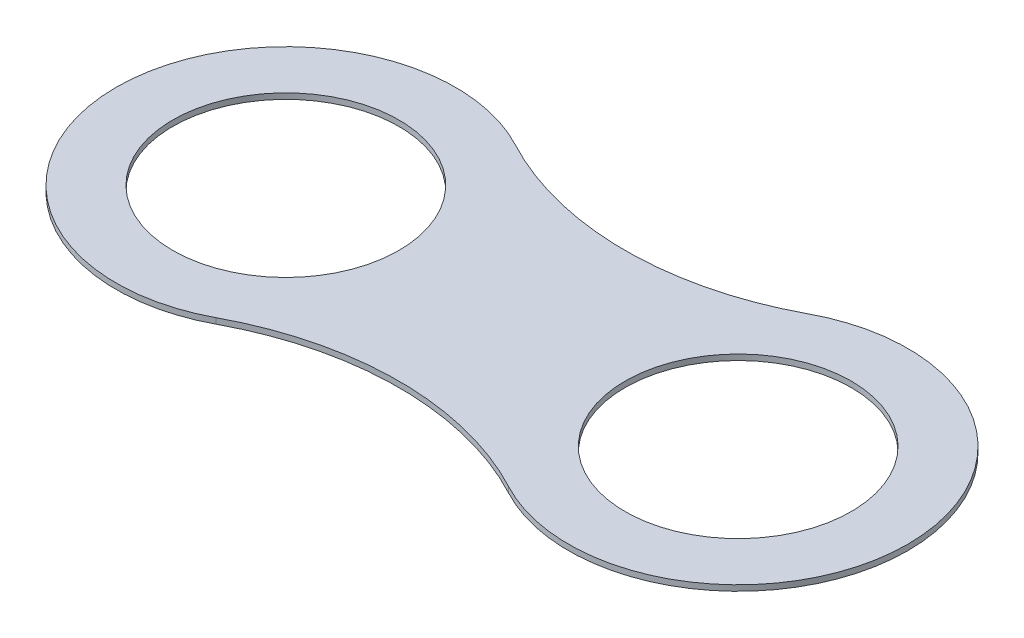
SolidWorks part; units mm, degrees
ref_plane "Face" through (0, 0, 0) normal (0, 0, 1) x (1, 0, 0)
ref_plane "Dessus" through (0, 0, 0) normal (0, 1, 0) x (1, 0, 0)
ref_plane "Droite" through (0, 0, 0) normal (1, 0, 0) x (0, 0, -1)
sketch "Esquisse1" plane through (0, 0, 0) normal (0, 1, 0) x (1, 0, 0)
  line L0 (0, 0) -> (800, 0) construction
  line L1 (400, 200) -> (400, 0) construction
  line L2 (0, 0) -> (-300, 0) construction
  arc A0 (141.1765, -264.7059) -> (141.1765, 264.7059) centre (0, 0) cw
  circle A1 centre (0, 0) radius 200
  arc A3 (141.1765, 264.7059) -> (658.8235, 264.7059) centre (400, 750) ccw
  arc A4 (141.1765, -264.7059) -> (658.8235, -264.7059) centre (400, -750) cw
  circle A5 centre (800, 0) radius 200
  arc A6 (658.8235, -264.7059) -> (658.8235, 264.7059) centre (800, 0) ccw
  point P6 (800, 0)
  dimension "D2" = 300
  dimension "D3" = 400
  dimension "D5" = 550
  dimension "D1" = 800
extrude "Extrusion1" add sketch "Esquisse1" along normal blind 10
